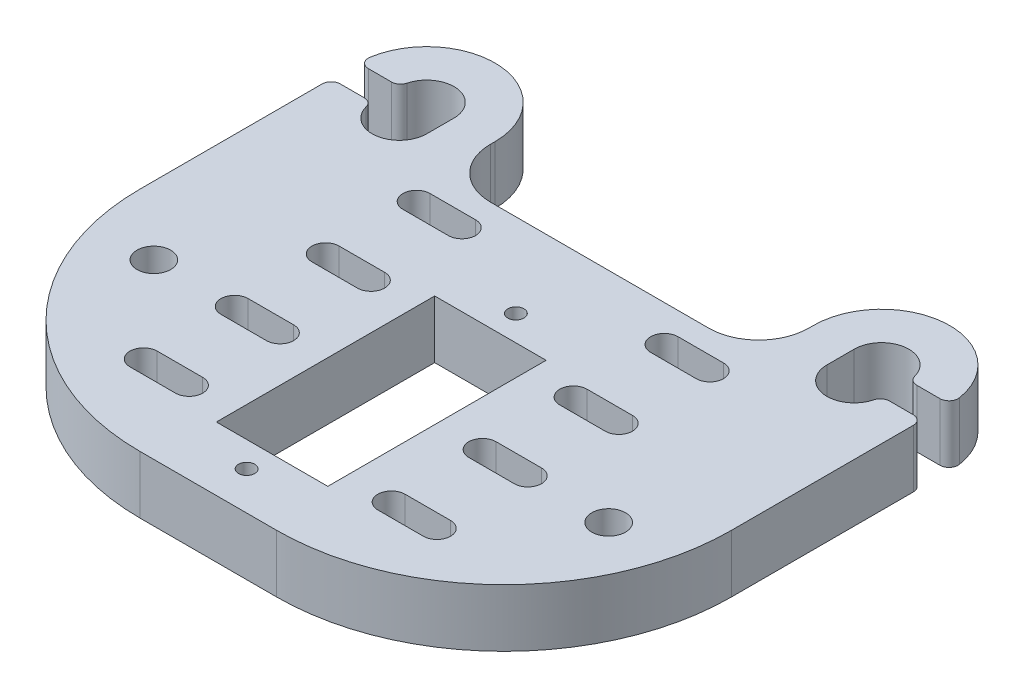
SolidWorks part; units mm, degrees
ref_plane "Front Plane" through (0, 0, 0) normal (0, 0, 1) x (1, 0, 0)
ref_plane "Top Plane" through (0, 0, 0) normal (0, 1, 0) x (1, 0, 0)
ref_plane "Right Plane" through (0, 0, 0) normal (1, 0, 0) x (0, 0, -1)
sketch "Sketch1" plane through (0, 0, 0) normal (0, 1, 0) x (1, 0, 0)
  line L0 (-25.796, 10.9144) -> (-25.796, 28.9144)
  line L1 (0.579, 16.9144) -> (12.829, 16.9144)
  line L2 (0.579, 16.9144) -> (0.579, -7.0856)
  line L3 (0.579, -7.0856) -> (12.829, -7.0856)
  line L4 (12.829, 16.9144) -> (12.829, -7.0856)
  line L5 (39.204, 10.9144) -> (39.204, 28.9144)
  line L6 (-18.296, 34.9144) -> (-18.296, 31.9144) construction
  line L7 (24.204, 34.9144) -> (24.204, 34.4144)
  line L8 (-10.796, 34.9144) -> (-10.796, 34.4144)
  line L9 (31.704, 31.9144) -> (31.704, 34.9144) construction
  line L11 (-9.421, 6.4144) -> (-4.421, 6.4144)
  line L12 (-18.296, 34.9144) -> (-18.296, 31.9144) construction
  line L13 (-0.796, -14.0856) -> (14.204, -14.0856)
  line L14 (-15.296, 34.9144) -> (-15.296, 31.9144)
  line L15 (-9.421, 3.4144) -> (-4.421, 3.4144)
  line L16 (31.704, 34.9144) -> (31.704, 31.9144) construction
  line L18 (28.704, 34.9144) -> (28.704, 31.9144)
  line L19 (-25.796, 30.9144) -> (-25.796, 28.9144)
  line L20 (39.204, 30.9144) -> (39.204, 28.9144)
  line L21 (22.829, 3.4144) -> (17.829, 3.4144)
  line L22 (22.829, 6.4144) -> (17.829, 6.4144)
  line L23 (-5.296, 28.9144) -> (18.704, 28.9144)
  line L24 (35.5769, 34.9144) -> (38.1266, 34.9144)
  line L25 (38.204, 31.9144) -> (35.5769, 31.9144)
  line L26 (-22.169, 31.9144) -> (-24.796, 31.9144)
  line L27 (-24.7187, 34.9144) -> (-22.169, 34.9144)
  line L29 (-9.421, -3.5856) -> (-4.421, -3.5856)
  line L30 (-9.421, -6.5856) -> (-4.421, -6.5856)
  line L32 (22.829, -6.5856) -> (17.829, -6.5856)
  line L33 (22.829, -3.5856) -> (17.829, -3.5856)
  line L35 (-9.421, 16.4144) -> (-4.421, 16.4144)
  line L36 (-9.421, 13.4144) -> (-4.421, 13.4144)
  line L38 (22.829, 13.4144) -> (17.829, 13.4144)
  line L39 (22.829, 16.4144) -> (17.829, 16.4144)
  line L41 (-9.421, 26.4144) -> (-4.421, 26.4144)
  line L42 (-9.421, 23.4144) -> (-4.421, 23.4144)
  line L44 (22.829, 23.4144) -> (17.829, 23.4144)
  line L45 (22.829, 26.4144) -> (17.829, 26.4144)
  circle A0 centre (6.704, 19.7144) radius 0.889
  circle A1 centre (6.704, -9.8856) radius 0.889
  arc A2 (-10.796, 34.9144) -> (-25.7068, 36.0683) centre (-18.296, 34.9144) ccw
  arc A3 (24.204, 34.4144) -> (18.704, 28.9144) centre (18.704, 34.4144) cw
  arc A4 (-10.796, 34.4144) -> (-5.296, 28.9144) centre (-5.296, 34.4144) ccw
  arc A5 (39.1147, 36.0683) -> (24.204, 34.9144) centre (31.704, 34.9144) ccw
  circle A6 centre (-18.296, 4.9144) radius 1.8529
  circle A7 centre (31.704, 4.9144) radius 1.8529
  arc A8 (14.204, -14.0856) -> (39.204, 10.9144) centre (14.204, 10.9144) ccw
  arc A9 (-25.796, 10.9144) -> (-0.796, -14.0856) centre (-0.796, 10.9144) ccw
  arc A10 (-15.296, 34.9144) -> (-21.2008, 35.6644) centre (-18.296, 34.9144) ccw
  arc A11 (-21.2008, 31.1644) -> (-15.296, 31.9144) centre (-18.296, 31.9144) ccw
  arc A12 (34.6087, 35.6644) -> (28.704, 34.9144) centre (31.704, 34.9144) ccw
  arc A13 (28.704, 31.9144) -> (34.6087, 31.1644) centre (31.704, 31.9144) ccw
  arc A14 (38.204, 31.9144) -> (39.204, 30.9144) centre (38.204, 30.9144) cw
  arc A15 (38.1266, 34.9144) -> (39.1147, 36.0683) centre (38.1266, 35.9144) ccw
  arc A16 (35.5769, 34.9144) -> (34.6087, 35.6644) centre (35.5769, 35.9144) cw
  arc A17 (35.5769, 31.9144) -> (34.6087, 31.1644) centre (35.5769, 30.9144) ccw
  arc A18 (-24.796, 31.9144) -> (-25.796, 30.9144) centre (-24.796, 30.9144) ccw
  arc A19 (-22.169, 31.9144) -> (-21.2008, 31.1644) centre (-22.169, 30.9144) cw
  arc A20 (-22.169, 34.9144) -> (-21.2008, 35.6644) centre (-22.169, 35.9144) ccw
  arc A21 (-24.7187, 34.9144) -> (-25.7068, 36.0683) centre (-24.7187, 35.9144) cw
  arc A22 (-9.421, 6.4144) -> (-9.421, 3.4144) centre (-9.421, 4.9144) ccw
  arc A23 (-4.421, 3.4144) -> (-4.421, 6.4144) centre (-4.421, 4.9144) ccw
  arc A24 (22.829, 3.4144) -> (22.829, 6.4144) centre (22.829, 4.9144) ccw
  arc A25 (17.829, 6.4144) -> (17.829, 3.4144) centre (17.829, 4.9144) ccw
  arc A26 (-9.421, -3.5856) -> (-9.421, -6.5856) centre (-9.421, -5.0856) ccw
  arc A27 (-4.421, -6.5856) -> (-4.421, -3.5856) centre (-4.421, -5.0856) ccw
  arc A28 (22.829, -6.5856) -> (22.829, -3.5856) centre (22.829, -5.0856) ccw
  arc A29 (17.829, -3.5856) -> (17.829, -6.5856) centre (17.829, -5.0856) ccw
  arc A30 (-9.421, 16.4144) -> (-9.421, 13.4144) centre (-9.421, 14.9144) ccw
  arc A31 (-4.421, 13.4144) -> (-4.421, 16.4144) centre (-4.421, 14.9144) ccw
  arc A32 (22.829, 13.4144) -> (22.829, 16.4144) centre (22.829, 14.9144) ccw
  arc A33 (17.829, 16.4144) -> (17.829, 13.4144) centre (17.829, 14.9144) ccw
  arc A34 (-9.421, 26.4144) -> (-9.421, 23.4144) centre (-9.421, 24.9144) ccw
  arc A35 (-4.421, 23.4144) -> (-4.421, 26.4144) centre (-4.421, 24.9144) ccw
  arc A36 (22.829, 23.4144) -> (22.829, 26.4144) centre (22.829, 24.9144) ccw
  arc A37 (17.829, 26.4144) -> (17.829, 23.4144) centre (17.829, 24.9144) ccw
  point P60 (-25.796, 31.9144)
  point P63 (-21.296, 31.9144)
  point P128 (-6.921, -5.0856)
  dimension "D3" = 2.8
  dimension "D4" = 2.8
  dimension "D5" = 1.778
  dimension "D6" = 1.778
  dimension "D7" = 3.7059
  dimension "D8" = 3.7059
  dimension "D15" = 7.5
  dimension "D16" = 7.5
  dimension "D24" = 25
  dimension "D25" = 7.5
  dimension "D26" = 65
  dimension "D31" = 5
  dimension "D32" = 1.5
  dimension "D21" = 3
  dimension "D27" = 7.5
  dimension "D28" = 7.5
  dimension "D29" = 3
  dimension "D30" = 3
  dimension "D11" = 5.5
  dimension "D22" = 1
  dimension "D33" = 1.5
  dimension "D2" = 12.25
  dimension "D9" = 25
  dimension "D10" = 25
  dimension "D12" = 24
  dimension "D13" = 5
  dimension "D14" = 5
  dimension "D17" = 6.125
  dimension "D18" = 6.125
  dimension "D19" = 7
  dimension "D23" = 5
  dimension "D20" = 3
extrude "Boss-Extrude1" add sketch "Sketch1" along normal blind 6.35
